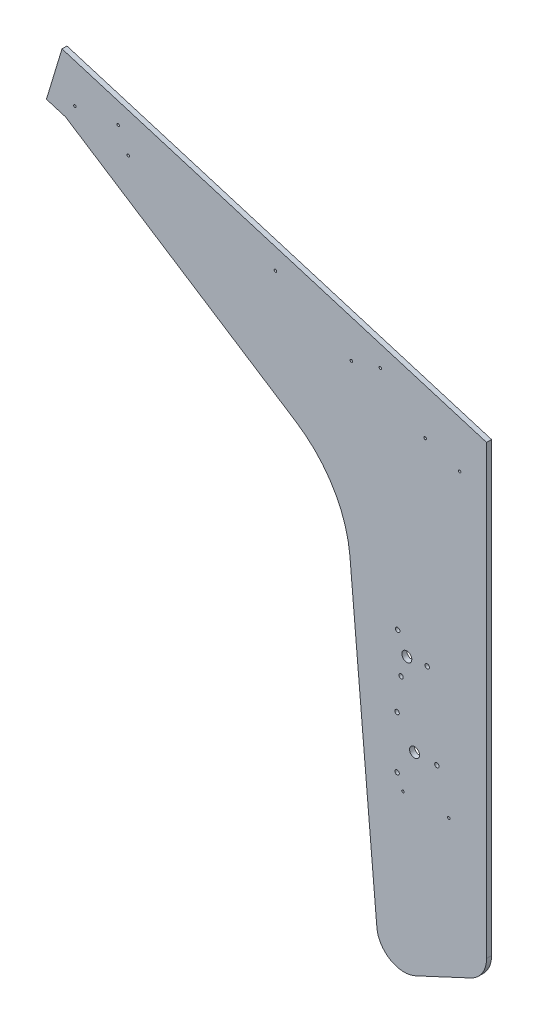
SolidWorks part; units mm, degrees
material "Beech"
ref_plane "Front Plane" through (0, 0, 0) normal (0, 0, 1) x (1, 0, 0)
ref_plane "Top Plane" through (0, 0, 0) normal (0, 1, 0) x (1, 0, 0)
ref_plane "Right Plane" through (0, 0, 0) normal (1, 0, 0) x (0, 0, -1)
sketch "Sketch1" plane through (0, 0, 0) normal (0, 0, 1) x (1, 0, 0)
  line L0 (-396.462, 396.5071) -> (138.3789, 234.6347) construction
  line L1 (134.7, 222.4793) -> (134.7, -217.5629) construction
  line L14 (-35.9297, 42.1538) -> (-1.5139, -351.2208)
  line L15 (48.0382, -379.8296) -> (118.2139, -347.1062)
  line L16 (138.3789, -315.4534) -> (138.3789, 254.5381)
  line L17 (138.3789, 254.5381) -> (-403.0991, 418.4193)
  line L18 (-403.0991, 418.4193) -> (-422.935, 352.8794)
  line L19 (-422.935, 352.8794) -> (-398.6241, 345.5216)
  line L20 (-398.6241, 345.5216) -> (-105.0266, 156.03)
  arc A6 (-35.9297, 42.1538) -> (-105.0266, 156.03) centre (-187.6695, 27.9835) ccw
  arc A7 (-1.5139, -351.2208) -> (48.0382, -379.8296) centre (33.2782, -348.1768) ccw
  arc A8 (118.2139, -347.1062) -> (138.3789, -315.4534) centre (103.4539, -315.4534) ccw
  dimension "D5" = 34.925
  dimension "D6" = 34.925
  dimension "D11" = 152.4
  dimension "D1" = 115
  dimension "D2" = 70
  dimension "D3" = 16
  dimension "D4" = 19.05
  dimension "D7" = 569.9915
  dimension "D8" = 602.715
  dimension "D9" = 34.925
  dimension "D10" = 105.1007
  dimension "D13" = 25.4
  dimension "D14" = 326.0484
  dimension "D15" = 226.5547
  dimension "D16" = 139.8928
  dimension "D17" = 77.4303
extrude "Boss-Extrude1" add sketch "Sketch1" along normal blind 6.35
hole_wizard "#10 Clearance Hole1" positions "Sketch3" profile "Sketch4" hole size "#10" standard "ANSI Inch" end condition through all
sketch "Sketch3" plane through (0, 0, 0) normal (0, 0, -1) x (-1, 0, 0)
  point P0 (-24.2517, -100.3519)
  point P3 (-24.2517, -167.0269)
  point P6 (-75.0517, -133.6894)
  point P9 (-29.3174, -58.2747)
  point P12 (-25.0263, -9.2271)
  point P15 (-62.6488, -30.6471)
sketch "Sketch4" plane through (24.2517, -100.3519, 0) normal (1, 0, 0) x (0, 1, 0)
  line L0 (0, 0) -> (0, 6.35)
  line L1 (0, 6.35) -> (2.8067, 6.35)
  line L2 (2.8067, 6.35) -> (2.8067, 0)
  line L5 (2.8067, 0) -> (0, 0)
  line L11 (0, -6.35) -> (0, 107.95) construction
  dimension "Thru Hole Dia." = 5.6134
  dimension "Thru Hole Depth" = 6.35
sketch "Sketch2" plane through (0, 0, 0) normal (0, 0, -1) x (-1, 0, 0)
  line L0 (-2.0267, -133.6894) -> (-59.1767, -133.6894) construction
  line L1 (-2.0267, -115.5093) -> (-2.0267, -151.8694) construction
  line L2 (-59.1767, -116.3297) -> (-59.1767, -151.0491) construction
  line L3 (-29.3174, -58.2747) -> (-25.0263, -9.2271) construction
  line L4 (-27.1718, -33.7509) -> (-62.6488, -30.6471) construction
  circle A0 centre (-46.4767, -133.6894) radius 6.35
  circle A1 centre (-36.6606, -32.9207) radius 6.35
  circle A2 centre (-24.2517, -100.3519) radius 2.8067 construction
  point P7 (-2.0267, -133.6894)
  point P11 (-59.1767, -133.6894)
  dimension "D1" = 12.7
  dimension "D2" = 12.7
  dimension "D3" = 22.225
  dimension "D4" = 9.525
extrude "Cut-Extrude1" cut sketch "Sketch2" against normal through all
hole_wizard "Hole1" positions "Sketch5" profile "Sketch6" legacy
sketch "Sketch5" plane through (277.2867, -215.2871, 12.7) normal (0, 0, 1) x (-0.09, 0.9959, 0)
  line L0 (54.6742, 260.7254) -> (44.8416, 151.8686) construction
  line L6 (458.2175, 188.8136) -> (426.7882, 117.3689) construction
  line L11 (486.0396, 272.5028) -> (513.4071, 262.4897) construction
  line L19 (643.2075, 626.7743) -> (602.3132, 525.5573) construction
  line L24 (664.0363, 618.3589) -> (454.7061, 100.2486) construction
  line L28 (664.0363, 618.3589) -> (611.7037, 488.8313)
  line L29 (611.7037, 488.8313) -> (559.3712, 359.3037)
  line L30 (559.3712, 359.3037) -> (507.0387, 229.7761)
  line L31 (507.0387, 229.7761) -> (454.7061, 100.2486)
  line L33 (513.4071, 262.4897) -> (486.0396, 272.5028)
  point P12 (52.9605, 241.7526)
  point P14 (47.6978, 183.4898)
  point P29 (434.4591, 134.8062)
  point P31 (453.1036, 177.1887)
  point P48 (499.7233, 267.4963)
  point P79 (636.0712, 609.1114)
  point P81 (609.4494, 543.2202)
  point P98 (559.3712, 359.3037)
  point P100 (507.0387, 229.7761)
  point P112 (637.87, 553.5951)
  point P122 (0, 0)
  point P126 (499.7233, 267.4963)
  point P127 (0, 0)
  point P128 (0, 0)
  point P129 (484.7752, 272.5028)
  dimension "D1" = 19.05
  dimension "D2" = 31.75
  dimension "D3" = 12.7
  dimension "D4" = 19.05
  dimension "D5" = 19.05
  dimension "D6" = 19.05
sketch "Sketch6" plane through (-331.4463, 370.1954, 12.7) normal (1, 0, 0) x (0, -1, 0)
  line L0 (0, 0) -> (0, 32.7039)
  line L1 (0, 32.7039) -> (1.5875, 31.75)
  line L2 (1.5875, 31.75) -> (1.5875, 4.0177)
  line L3 (1.5875, 4.0177) -> (5.08, 0)
  line L4 (5.08, 0) -> (0, 0)
  line L5 (0, -14.3089) -> (0, 102.4216) construction
  line L6 (0, 32.7039) -> (-1.5875, 31.75) construction
  line L7 (-1.5875, 4.0177) -> (-5.08, 0) construction
  dimension "Diameter" = 3.175
  dimension "Depth" = 31.75
  dimension "C-Sink Diameter" = 10.16
  dimension "C-Sink Angle" = 82
  dimension "Drill Angle" = 118
